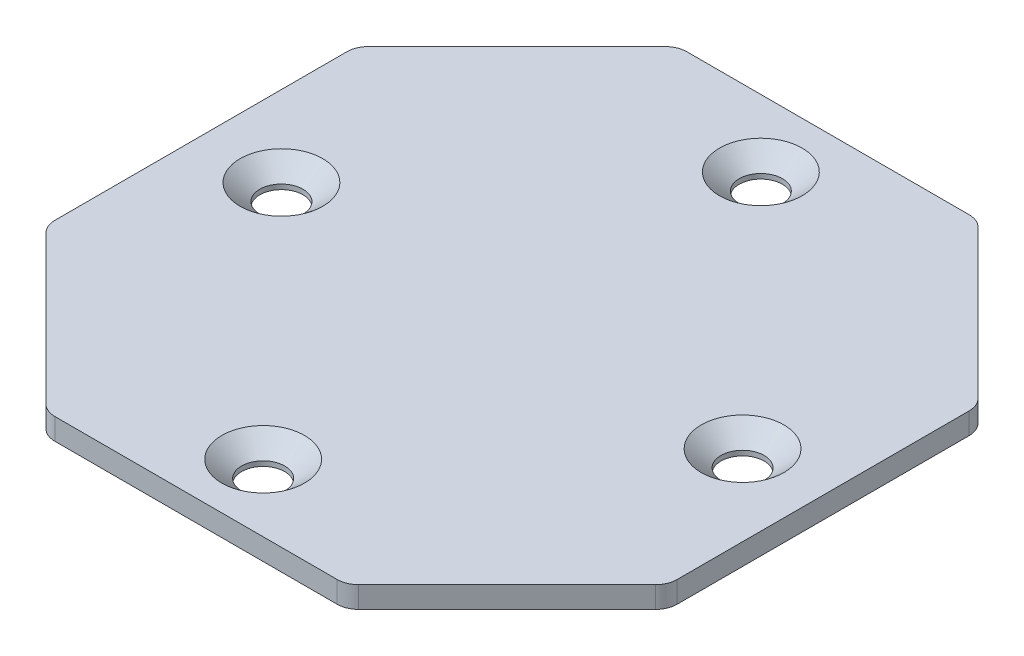
SolidWorks part; units mm, degrees
ref_plane "Front Plane" through (0, 0, 0) normal (0, 0, 1) x (1, 0, 0)
ref_plane "Top Plane" through (0, 0, 0) normal (0, 1, 0) x (1, 0, 0)
ref_plane "Right Plane" through (0, 0, 0) normal (1, 0, 0) x (0, 0, -1)
sketch "Main_Base_Dim" plane through (0, 0, 0) normal (0, 1, 0) x (1, 0, 0)
  line L1 (0, 0) -> (73.6, 0)
  line L2 (0, 0) -> (0, 74.75)
  line L3 (0, 74.75) -> (73.6, 74.75)
  line L4 (73.6, 0) -> (73.6, 74.75)
  dimension "D1" = 73.6
  dimension "D2" = 74.75
extrude "Main_Base" add sketch "Main_Base_Dim" along normal blind 2.54
sketch "Hole_Placement" plane through (0, 2.54, 0) normal (0, 1, 0) x (1, 0, 0)
  line L0 (0, 74.75) -> (0, 0) construction
  line L1 (19.05, 58.875) -> (54.55, 58.875) construction
  line L2 (19.05, 58.875) -> (19.05, 15.875) construction
  line L3 (19.05, 15.875) -> (54.55, 15.875) construction
  line L4 (54.55, 58.875) -> (54.55, 15.875) construction
  line L5 (73.6, 74.75) -> (0, 74.75) construction
  line L6 (36.8, 58.875) -> (36.8, 74.75) construction
  line L7 (54.55, 37.375) -> (73.6, 37.375) construction
  line L8 (73.6, 0) -> (73.6, 74.75) construction
  line L9 (36.8, 15.875) -> (36.8, 0) construction
  line L10 (0, 0) -> (73.6, 0) construction
  line L11 (19.05, 37.375) -> (0, 37.375) construction
  circle A0 centre (9.525, 37.375) radius 2.5812
  circle A1 centre (64.075, 37.375) radius 2.5812
  circle A2 centre (36.8, 66.8125) radius 2.5812
  circle A3 centre (36.8, 7.9375) radius 2.5812
  point P6 (0, 37.375)
  point P7 (19.05, 37.375)
  point P10 (36.8, 74.75)
  point P11 (36.8, 58.875)
  dimension "D1" = 35.5
  dimension "D3" = 43
hole_wizard "CSK for #10 Flat Head Machine Screw (100)1" positions "3DSketch2" profile "Sketch4" countersink size "#10" standard "ANSI Inch" end condition through all
sketch3d "3DSketch2"
  point P0 (9.525, 2.54, -37.375)
  point P3 (36.8, 2.54, -7.9375)
  point P6 (64.075, 2.54, -37.375)
  point P9 (36.8, 2.54, -66.8125)
sketch "Sketch4" plane through (9.525, 2.54, -37.375) normal (1, 0, 0) x (0, 0, 1)
  line L0 (0, 0) -> (0, 2.54)
  line L1 (0, 2.54) -> (2.5527, 2.54)
  line L2 (2.5527, 2.54) -> (2.5527, 1.9608)
  line L3 (2.5527, 1.9608) -> (4.8895, 0)
  line L5 (4.8895, 0) -> (0, 0)
  line L6 (-2.5527, 1.9608) -> (-4.8895, 0) construction
  line L11 (0, -6.35) -> (0, 107.95) construction
  dimension "Thru Hole Dia." = 5.1054
  dimension "Thru Hole Depth" = 2.54
  dimension "Near C'Sink Dia." = 9.779
  dimension "Near C'Sink Angle" = 100
sketch "Corner_Cut_Dim" plane through (0, 2.54, 0) normal (0, 1, 0) x (1, 0, 0)
  line L0 (0, 0) -> (0, 19.05)
  line L1 (0, 74.75) -> (0, 0) construction
  line L2 (0, 19.05) -> (19.05, 0)
  line L3 (0, 0) -> (73.6, 0) construction
  line L4 (19.05, 0) -> (0, 0)
  line L5 (36.8, 74.75) -> (36.8, 0) construction
  line L6 (73.6, 74.75) -> (0, 74.75) construction
  line L7 (0, 37.375) -> (73.6, 37.375) construction
  line L8 (73.6, 0) -> (73.6, 74.75) construction
  line L9 (54.55, 0) -> (73.6, 0)
  line L10 (73.6, 19.05) -> (54.55, 0)
  line L11 (73.6, 0) -> (73.6, 19.05)
  line L12 (73.6, 74.75) -> (73.6, 55.7)
  line L13 (54.55, 74.75) -> (73.6, 74.75)
  line L14 (73.6, 55.7) -> (54.55, 74.75)
  line L15 (0, 55.7) -> (19.05, 74.75)
  line L16 (0, 74.75) -> (0, 55.7)
  line L17 (19.05, 74.75) -> (0, 74.75)
  dimension "D1" = 19.05
  dimension "D2" = 19.05
extrude "Coner_Cut" cut sketch "Corner_Cut_Dim" against normal up to surface (2.54 mm away) up to face at (9.525, 0, -34.8223)
fillet ".1in_Fillet" radius 2.54 8 edges at (73.6, 1.27, -19.05) (73.6, 1.27, -55.7) (54.55, 1.27, -74.75) (19.05, 1.27, -74.75) (0, 1.27, -55.7) (0, 1.27, -19.05) (19.05, 1.27, 0) (54.55, 1.27, 0)
